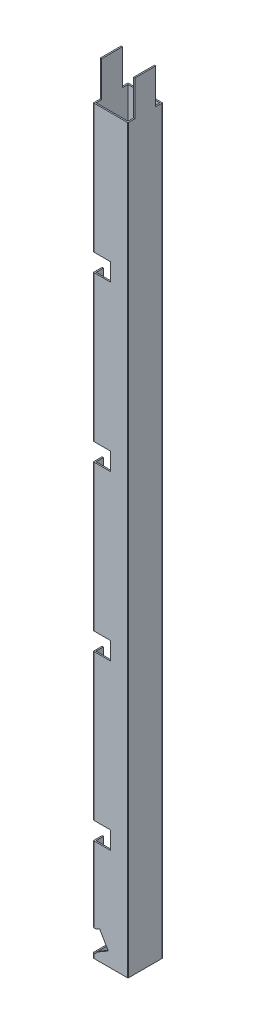
SolidWorks part; units mm, degrees
ref_plane "Front Plane" through (0, 0, 0) normal (0, 0, 1) x (1, 0, 0)
ref_plane "Top Plane" through (0, 0, 0) normal (0, 1, 0) x (1, 0, 0)
ref_plane "Right Plane" through (0, 0, 0) normal (1, 0, 0) x (0, 0, -1)
sketch "Sketch1" plane through (0, 0, 0) normal (0, 1, 0) x (1, 0, 0)
  line L0 (1.5, 1.5) -> (38.5, 1.5)
  line L1 (0.5, 0) -> (39.5, 0)
  line L2 (0, 0.5) -> (0, 39.5)
  line L3 (0.5, 40) -> (39.5, 40)
  line L4 (40, 0.5) -> (40, 39.5)
  line L5 (38.5, 1.5) -> (38.5, 38.5)
  line L6 (1.5, 38.5) -> (38.5, 38.5)
  line L7 (1.5, 1.5) -> (1.5, 38.5)
  arc A0 (39.5, 0) -> (40, 0.5) centre (39.5, 0.5) ccw
  arc A1 (0.5, 0) -> (0, 0.5) centre (0.5, 0.5) cw
  arc A2 (0, 39.5) -> (0.5, 40) centre (0.5, 39.5) cw
  arc A3 (39.5, 40) -> (40, 39.5) centre (39.5, 39.5) cw
  arc A4 (38.5, 1.5) -> (38.5, 1.5) centre (38.5, 1.5) ccw
  arc A5 (38.5, 38.5) -> (38.5, 38.5) centre (38.5, 38.5) cw
  arc A6 (1.5, 38.5) -> (1.5, 38.5) centre (1.5, 38.5) cw
  arc A7 (1.5, 1.5) -> (1.5, 1.5) centre (1.5, 1.5) cw
  point P9 (0, 0)
  dimension "D3" = 0.5
  dimension "D1" = 40
  dimension "D2" = 40
  dimension "D4" = 1.5
extrude "Boss-Extrude1" add sketch "Sketch1" along normal blind 899
sketch "Sketch3" plane through (0, 0, 0) normal (0, 0, 1) x (1, 0, 0)
  line L10 (39.5, 899) -> (39.5, 0) construction
  line L12 (20, 0) -> (20, 27.3534) construction
  line L13 (0.5, 0) -> (39.5, 0) construction
  line L15 (0, 29.0143) -> (0, 5.9073)
  line L16 (0, 30.7464) -> (0, 29.0143)
  line L17 (0, 30.7464) -> (3, 30.7464)
  line L18 (7.0729, 33.0986) -> (3, 30.7464)
  line L19 (7.0729, 33.0986) -> (17.1255, 15.7976)
  line L20 (3, 7.6398) -> (17.1255, 15.7976)
  line L21 (3, 5.9073) -> (3, 7.6398)
  line L22 (0, 5.9073) -> (3, 5.9073)
  dimension "D1" = 22.3745
  dimension "D2" = 32.4271
  dimension "D3" = 36.5
  dimension "D4" = 39.5
  dimension "D5" = 5.9073
  dimension "D6" = 7.6398
  dimension "D7" = 15.7976
  dimension "D8" = 29.0143
  dimension "D9" = 30.7464
  dimension "D11" = 899
extrude "Cut-Extrude2" cut sketch "Sketch3" against normal blind 20
sketch "Sketch4" plane through (0, 0, 0) normal (-1, 0, 0) x (0, 0, 1)
  line L1 (0, 899) -> (-8, 899)
  line L2 (0, 899) -> (0, 858)
  line L3 (0, 858) -> (-8, 858)
  line L4 (-8, 899) -> (-8, 858)
  line L5 (-40, 899) -> (-32, 899)
  line L6 (-40, 899) -> (-40, 858)
  line L7 (-40, 858) -> (-32, 858)
  line L8 (-32, 899) -> (-32, 858)
  dimension "D1" = 8
  dimension "D2" = 41
  dimension "D3" = 41
extrude "Cut-Extrude3" cut sketch "Sketch4" against normal through all
sketch "Sketch5" plane through (0, 0, -40) normal (0, 0, -1) x (-1, 0, 0)
  line L0 (-39.5, 0) -> (-0.5, 0) construction
  line L1 (0, 858) -> (0, 0) construction
  circle A0 centre (-10, 30) radius 3.5
  circle A1 centre (-10, 15) radius 3.5
  dimension "D1" = 15
  dimension "D2" = 15
  dimension "D3" = 7
  dimension "D4" = 10
extrude "Cut-Extrude4" cut sketch "Sketch5" against normal blind 10
sketch "Sketch6" plane through (0, 0, 0) normal (-1, 0, 0) x (0, 0, 1)
  line L0 (0, 708.5) -> (-20, 708.5)
  line L1 (0, 858) -> (0, 30.7464) construction
  line L2 (-20, 708.5) -> (-20, 668)
  line L3 (-20, 668) -> (-10, 668)
  line L4 (-10, 668) -> (-10, 688)
  line L5 (-10, 688) -> (0, 688)
  line L6 (0, 688) -> (0, 708.5)
  line L7 (-8, 858) -> (-0.5, 858) construction
  line L8 (0, 518.5) -> (-20, 518.5)
  line L9 (-20, 518.5) -> (-20, 478)
  line L10 (-20, 478) -> (-10, 478)
  line L11 (-10, 478) -> (-10, 498)
  line L12 (-10, 498) -> (0, 498)
  line L13 (0, 498) -> (0, 518.5)
  line L14 (0, 328.5) -> (-20, 328.5)
  line L15 (-20, 328.5) -> (-20, 288)
  line L16 (-20, 288) -> (-10, 288)
  line L17 (-10, 288) -> (-10, 308)
  line L18 (-10, 308) -> (0, 308)
  line L19 (0, 308) -> (0, 328.5)
  line L20 (0, 138.5) -> (-20, 138.5)
  line L21 (-20, 138.5) -> (-20, 98)
  line L22 (-20, 98) -> (-10, 98)
  line L23 (-10, 98) -> (-10, 118)
  line L24 (-10, 118) -> (0, 118)
  line L25 (0, 118) -> (0, 138.5)
  dimension "D1" = 20
  dimension "D2" = 10
  dimension "D3" = 20
  dimension "D4" = 20.5
  dimension "D5" = 170
  dimension "D6" = 4
extrude "Cut-Extrude5" cut sketch "Sketch6" against normal blind 20
